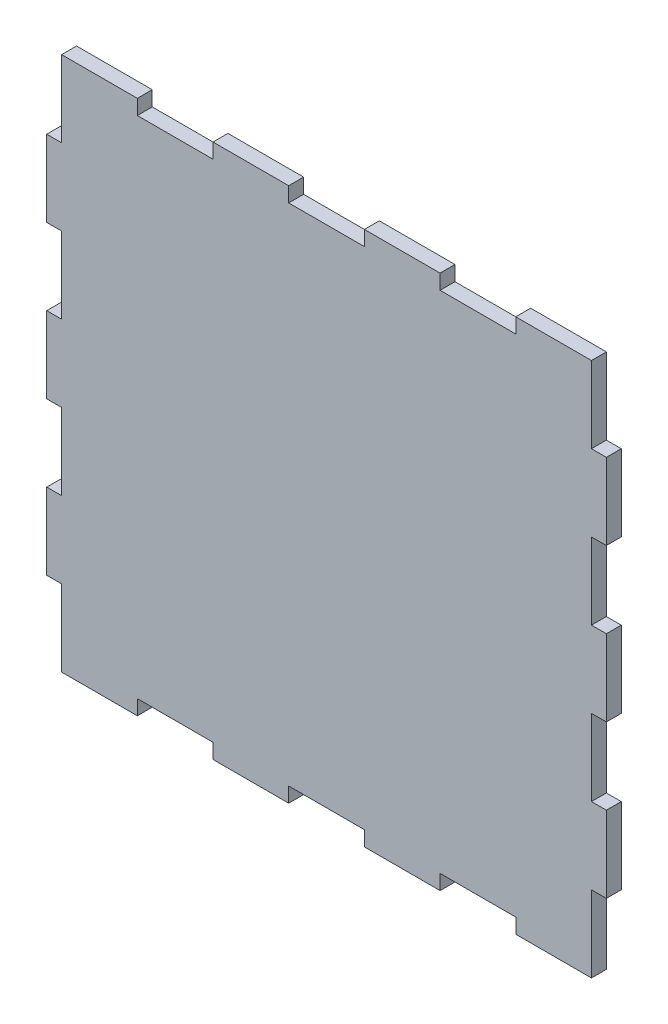
SolidWorks part; units mm, degrees
ref_plane "Alzado" through (0, 0, 0) normal (0, 0, 1) x (1, 0, 0)
ref_plane "Planta" through (0, 0, 0) normal (0, 1, 0) x (1, 0, 0)
ref_plane "Vista lateral" through (0, 0, 0) normal (1, 0, 0) x (0, 0, -1)
sketch "Croquis1" plane through (0, 0, 0) normal (0, 0, 1) x (1, 0, 0)
  line L0 (-76.15, 28.8494) -> (-76.15, -51.02) construction
  line L1 (-79.15, 18.6361) -> (33.46, 18.6361) construction
  line L2 (-79.15, 18.6361) -> (-79.15, -31.3639) construction
  line L3 (-79.15, -31.3639) -> (33.46, -31.3639) construction
  line L4 (33.46, 18.6361) -> (33.46, -31.3639) construction
  line L5 (30.46, 26.8438) -> (30.46, -48.3082) construction
  line L6 (-85.6573, -28.3639) -> (41.9564, -28.3639) construction
  line L7 (-99.0946, 15.6361) -> (68.6346, 15.6361) construction
  line L8 (-71.15, -28.3639) -> (-71.15, -31.3639)
  line L9 (25.46, -28.3639) -> (25.46, -31.3639)
  line L10 (-71.15, -31.3639) -> (25.46, -31.3639)
  line L11 (-71.15, -28.3639) -> (-76.15, -28.3639)
  line L12 (-76.15, -28.3639) -> (-76.15, -31.3639)
  line L13 (-76.15, -31.3639) -> (-79.15, -31.3639)
  line L14 (25.46, -28.3639) -> (30.46, -28.3639)
  line L15 (30.46, -28.3639) -> (30.46, -31.3639)
  line L16 (30.46, -31.3639) -> (33.46, -31.3639)
  line L17 (33.46, -31.3639) -> (33.46, -19.6139)
  line L18 (33.46, -19.6139) -> (30.46, -19.6139)
  line L19 (30.46, -19.6139) -> (30.46, -7.8639)
  line L20 (30.46, -7.8639) -> (33.46, -7.8639)
  line L21 (33.46, -7.8639) -> (33.46, 3.8861)
  line L22 (33.46, 3.8861) -> (30.46, 3.8861)
  line L23 (30.46, 3.8861) -> (30.46, 15.6361)
  line L24 (30.46, 15.6361) -> (15.23, 15.6361)
  line L25 (15.23, 15.6361) -> (15.23, 18.6361)
  line L26 (15.23, 18.6361) -> (0, 18.6361)
  line L27 (0, 18.6361) -> (0, 15.6361)
  line L28 (0, 15.6361) -> (-15.23, 15.6361)
  line L29 (-15.23, 15.6361) -> (-15.23, 18.6361)
  line L30 (-15.23, 18.6361) -> (-30.46, 18.6361)
  line L31 (-30.46, 18.6361) -> (-30.46, 15.6361)
  line L32 (-30.46, 15.6361) -> (-45.69, 15.6361)
  line L33 (-45.69, 15.6361) -> (-45.69, 18.6361)
  line L34 (-45.69, 18.6361) -> (-60.92, 18.6361)
  line L35 (-60.92, 18.6361) -> (-60.92, 15.6361)
  line L36 (-60.92, 15.6361) -> (-76.15, 15.6361)
  line L37 (-79.15, -31.3639) -> (-79.15, -19.6139)
  line L38 (-79.15, -19.6139) -> (-76.15, -19.6139)
  line L39 (-76.15, -19.6139) -> (-76.15, -7.8639)
  line L40 (-76.15, -7.8639) -> (-79.15, -7.8639)
  line L41 (-79.15, -7.8639) -> (-79.15, 3.8861)
  line L42 (-79.15, 3.8861) -> (-76.15, 3.8861)
  line L43 (-76.15, 3.8861) -> (-76.15, 15.6361)
  line L44 (138.6179, 261.633) -> (138.6179, -48.3185) construction
  line L45 (141.6179, 35.2642) -> (141.6179, -48.3185) construction
  line L46 (243.2279, 33.3064) -> (243.2279, -51.0303) construction
  line L47 (246.2279, 143.2673) -> (246.2279, -57.2157) construction
  line L48 (243.2279, -31.3639) -> (141.6179, -31.3639)
  line L49 (141.6179, -31.3639) -> (141.6179, -19.6139)
  line L50 (141.6179, -19.6139) -> (138.6179, -19.6139)
  line L51 (138.6179, -19.6139) -> (138.6179, -6.5272)
  line L52 (138.6179, -6.5272) -> (141.6179, -6.5272)
  line L53 (141.6179, -6.5272) -> (141.6179, 3.8861)
  line L54 (141.6179, 3.8861) -> (138.6179, 3.8861)
  line L55 (138.6179, 3.8861) -> (138.6179, 18.6361)
  line L56 (109.4401, 103.7223) -> (113.3913, 103.7223) construction
  line L57 (138.6179, 211.3323) -> (-4.8813, 211.3323) construction
  line L58 (243.2279, -31.3639) -> (243.2279, -19.6139)
  line L59 (-76.15, 195.9594) -> (-76.15, 211.3323)
  line L60 (30.46, 211.3323) -> (30.46, 195.9594)
  line L61 (-76.15, 106.7223) -> (30.46, 106.7223) construction
  line L62 (30.46, 208.3321) -> (30.46, 106.7221) construction
  line L63 (243.2279, -19.6139) -> (246.2279, -19.6139)
  line L64 (246.2279, -19.6139) -> (246.2279, -6.5272)
  line L65 (246.2279, -6.5272) -> (243.2279, -6.5272)
  line L66 (243.2279, -6.5272) -> (243.2279, 3.8861)
  line L67 (243.2279, 3.8861) -> (246.2279, 3.8861)
  line L68 (246.2279, 3.8861) -> (246.2279, 18.6361)
  line L69 (138.6179, 18.6361) -> (153.9908, 18.6361)
  line L70 (153.9908, 18.6361) -> (153.9908, 15.6361)
  line L71 (153.9908, 15.6361) -> (169.3636, 15.6361)
  line L72 (169.3636, 15.6361) -> (169.3636, 18.6361)
  line L73 (169.3636, 18.6361) -> (184.7365, 18.6361)
  line L74 (184.7365, 18.6361) -> (184.7365, 15.6361)
  line L75 (184.7365, 15.6361) -> (200.1093, 15.6361)
  line L76 (200.1093, 15.6361) -> (200.1093, 18.6361)
  line L77 (200.1093, 18.6361) -> (215.4822, 18.6361)
  line L78 (215.4822, 18.6361) -> (215.4822, 15.6361)
  line L79 (215.4822, 15.6361) -> (230.855, 15.6361)
  line L80 (230.855, 15.6361) -> (230.855, 18.6361)
  line L81 (230.855, 18.6361) -> (246.2279, 18.6361)
  line L82 (138.6179, 195.9594) -> (-142.1003, 195.9594) construction
  line L83 (138.6179, 180.5865) -> (-142.1003, 180.5865) construction
  line L84 (138.6179, 165.2137) -> (-133.8306, 165.2137) construction
  line L85 (138.6179, 149.8408) -> (-118.3699, 149.8408) construction
  line L86 (138.6179, 134.468) -> (-142.1003, 134.468) construction
  line L87 (138.6179, 119.0951) -> (-118.3699, 119.0951) construction
  line L88 (-76.15, 119.0951) -> (-76.15, 106.7223)
  line L89 (30.46, 119.0951) -> (33.46, 119.0951)
  line L90 (33.46, 119.0951) -> (33.46, 134.468)
  line L91 (33.46, 134.468) -> (30.46, 134.468)
  line L92 (30.46, 134.468) -> (30.46, 149.8408)
  line L93 (30.46, 149.8408) -> (33.46, 149.8408)
  line L94 (33.46, 149.8408) -> (33.46, 165.2137)
  line L95 (33.46, 165.2137) -> (30.46, 165.2137)
  line L96 (30.46, 165.2137) -> (30.46, 180.5865)
  line L97 (30.46, 180.5865) -> (33.46, 180.5865)
  line L98 (33.46, 180.5865) -> (33.46, 195.9594)
  line L99 (33.46, 195.9594) -> (30.46, 195.9594)
  line L100 (15.23, 103.7223) -> (30.46, 103.7223)
  line L101 (230.855, 18.6361) -> (230.855, 103.7223) construction
  line L102 (215.4822, 18.6361) -> (215.4822, 103.7223) construction
  line L103 (200.1093, 18.6361) -> (200.1093, 103.7223) construction
  line L104 (184.7365, 18.6361) -> (184.7365, 103.7223) construction
  line L105 (169.3636, 18.6361) -> (169.3636, 103.7223) construction
  line L106 (153.9908, 18.6361) -> (153.9908, 103.7223) construction
  line L107 (30.46, 106.7223) -> (30.46, 103.7223)
  line L108 (15.23, 103.7223) -> (15.23, 106.7223)
  line L109 (15.23, 106.7223) -> (0, 106.7223)
  line L110 (0, 106.7223) -> (0, 103.7223)
  line L111 (0, 103.7223) -> (-15.23, 103.7223)
  line L112 (-15.23, 103.7223) -> (-15.23, 106.7223)
  line L113 (-15.23, 106.7223) -> (-30.46, 106.7223)
  line L114 (-30.46, 106.7223) -> (-30.46, 103.7223)
  line L115 (-30.46, 103.7223) -> (-45.69, 103.7223)
  line L116 (-45.69, 103.7223) -> (-45.69, 106.7223)
  line L117 (-45.69, 106.7223) -> (-60.92, 106.7223)
  line L118 (-60.92, 106.7223) -> (-60.92, 103.7223)
  line L119 (-60.92, 103.7223) -> (-76.15, 103.7223)
  line L121 (-76.15, 119.0951) -> (-79.15, 119.0951)
  line L122 (-79.15, 119.0951) -> (-79.15, 134.468)
  line L123 (-79.15, 134.468) -> (-76.15, 134.468)
  line L124 (-76.15, 134.468) -> (-76.15, 149.8408)
  line L125 (-76.15, 149.8408) -> (-79.15, 149.8408)
  line L126 (-79.15, 149.8408) -> (-79.15, 165.2137)
  line L127 (-79.15, 165.2137) -> (-76.15, 165.2137)
  line L128 (-76.15, 165.2137) -> (-76.15, 180.5865)
  line L129 (-76.15, 180.5865) -> (-79.15, 180.5865)
  line L130 (-79.15, 180.5865) -> (-79.15, 195.9594)
  line L131 (-79.15, 195.9594) -> (-76.15, 195.9594)
  line L133 (-76.15, 211.3323) -> (-60.92, 211.3323)
  line L134 (-60.92, 211.3323) -> (-60.92, 208.3323)
  line L135 (-60.92, 208.3323) -> (-45.69, 208.3323)
  line L136 (-45.69, 208.3323) -> (-45.69, 211.3323)
  line L137 (-45.69, 211.3323) -> (-30.46, 211.3323)
  line L138 (-30.46, 211.3323) -> (-30.46, 208.3323)
  line L139 (-30.46, 208.3323) -> (-15.23, 208.3323)
  line L140 (-15.23, 208.3323) -> (-15.23, 211.3323)
  line L141 (-15.23, 211.3323) -> (0, 211.3323)
  line L142 (0, 211.3323) -> (0, 208.3323)
  line L143 (0, 208.3323) -> (15.23, 208.3323)
  line L144 (15.23, 208.3323) -> (15.23, 211.3323)
  line L145 (15.23, 211.3323) -> (30.46, 211.3323)
  line L146 (30.46, 106.7223) -> (30.46, 119.0951)
  line L147 (-76.15, 103.7223) -> (-76.15, 106.7223)
  arc A0 (246.2279, 103.7223) -> (138.6179, 211.3323) centre (138.6179, 103.7223) ccw construction
  arc A1 (230.855, 103.7223) -> (138.6179, 195.9594) centre (138.6179, 103.7223) ccw construction
  arc A2 (215.4822, 103.7223) -> (138.6179, 180.5865) centre (138.6179, 103.7223) ccw construction
  arc A3 (200.1093, 103.7223) -> (138.6179, 165.2137) centre (138.6179, 103.7223) ccw construction
  arc A4 (184.7365, 103.7223) -> (138.6179, 149.8408) centre (138.6179, 103.7223) ccw construction
  arc A5 (169.3636, 103.7223) -> (138.6179, 134.468) centre (138.6179, 103.7223) ccw construction
  arc A6 (153.9908, 103.7223) -> (138.6179, 119.0951) centre (138.6179, 103.7223) ccw construction
  dimension "D1" = 112.61
  dimension "D3" = 3
  dimension "D4" = 3
  dimension "D5" = 3
  dimension "D6" = 3
  dimension "D7" = 5
  dimension "D8" = 5
  dimension "D9" = 3
  dimension "D10" = 3
  dimension "D11" = 107.61
  dimension "D12" = 3
  dimension "D14" = 3
extrude "Saliente-Extruir1" add sketch "Croquis1" along normal blind 3
